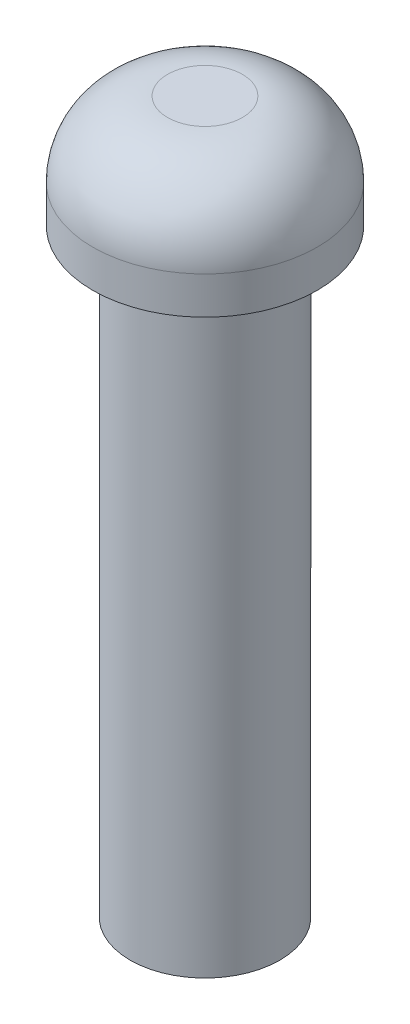
SolidWorks part; units mm, degrees
ref_plane "Plan de face" through (0, 0, 0) normal (0, 0, 1) x (1, 0, 0)
ref_plane "Plan de dessus" through (0, 0, 0) normal (0, 1, 0) x (1, 0, 0)
ref_plane "Plan de droite" through (0, 0, 0) normal (1, 0, 0) x (0, 0, -1)
sketch "Esquisse1" plane through (0, 0, 0) normal (0, 1, 0) x (1, 0, 0)
  circle A0 centre (0, 0) radius 15
extrude "Boss.-Extru.1" add sketch "Esquisse1" along normal blind 15
fillet "Congé1" radius 10 1 edges at (0, 15, 15)
sketch "Esquisse3" plane through (0, 0, 0) normal (0, -1, 0) x (1, 0, 0)
  circle A0 centre (0, 0) radius 10
extrude "Boss.-Extru.2" add sketch "Esquisse3" along normal blind 80
